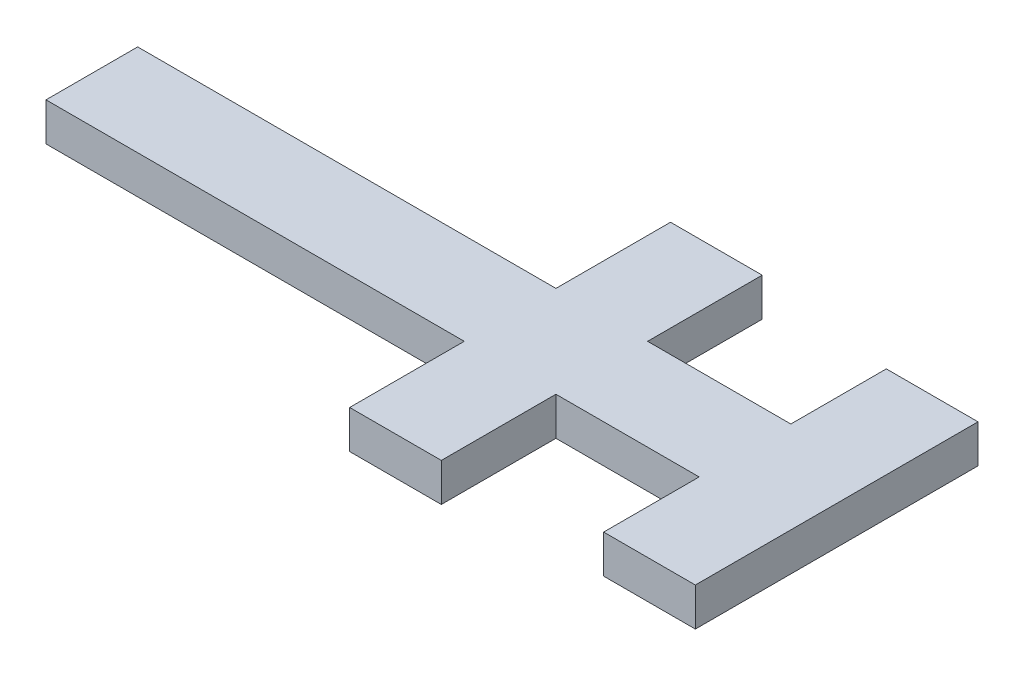
SolidWorks part; units mm, degrees
ref_plane "前视基准面" through (0, 0, 0) normal (0, 0, 1) x (1, 0, 0)
ref_plane "上视基准面" through (0, 0, 0) normal (0, 1, 0) x (1, 0, 0)
ref_plane "右视基准面" through (0, 0, 0) normal (1, 0, 0) x (0, 0, -1)
other "Configuration Table"
sketch "草图2" plane through (0, 0, 0) normal (0, 1, 0) x (1, 0, 0)
  line L0 (0, 0) -> (-31, 0) construction
  line L5 (-12.5, -5) -> (12.5, -5)
  line L6 (-12.5, -5) -> (-12.5, 5)
  line L7 (-12.5, 5) -> (12.5, 5)
  line L8 (12.5, -5) -> (12.5, 5)
  line L9 (-12.5, -5) -> (12.5, 5) construction
  line L10 (-12.5, 5) -> (12.5, -5) construction
  line L11 (17.5, 0) -> (12.5, 0) construction
  line L12 (-14, -5) -> (-48, -5)
  line L13 (-14, -5) -> (-14, 5)
  line L14 (-14, 5) -> (-48, 5)
  line L15 (-48, -5) -> (-48, 5)
  line L16 (-14, -5) -> (-48, 5) construction
  line L17 (-14, 5) -> (-48, -5) construction
  line L18 (-8.25, -20) -> (-18.25, -20)
  line L19 (-8.25, -20) -> (-8.25, 20)
  line L20 (-8.25, 20) -> (-18.25, 20)
  line L21 (-18.25, -20) -> (-18.25, 20)
  line L22 (-8.25, -20) -> (-18.25, 20) construction
  line L23 (-8.25, 20) -> (-18.25, -20) construction
  line L24 (22.5, -17.5) -> (12.5, -17.5)
  line L25 (22.5, -17.5) -> (22.5, 17.5)
  line L26 (22.5, 17.5) -> (12.5, 17.5)
  line L27 (12.5, -17.5) -> (12.5, 17.5)
  line L28 (22.5, -17.5) -> (12.5, 17.5) construction
  line L29 (22.5, 17.5) -> (12.5, -17.5) construction
  line L31 (-48, 5) -> (-73, 5)
  line L32 (-48, 5) -> (-48, -5)
  line L33 (-48, -5) -> (-73, -5)
  line L34 (-73, 5) -> (-73, -5)
  point P0 (0, 0)
  point P13 (17.5, 0)
  point P15 (-13.25, 0)
  dimension "D1" = 10
  dimension "D2" = 25
  dimension "D3" = 34
  dimension "D4" = 10
  dimension "D5" = 31
  dimension "D6" = 10
  dimension "D7" = 0.75
  dimension "D8" = 40
  dimension "D9" = 10
  dimension "D10" = 5
  dimension "D11" = 35
  dimension "D12" = 25
sketch "草图3" plane through (0, 0, 0) normal (0, 1, 0) x (1, 0, 0)
  line L0 (-12.5, -5) -> (12.5, -5) construction
  line L1 (22.5, 17.5) -> (12.5, 17.5)
  line L2 (22.5, 17.5) -> (22.5, -17.5)
  line L3 (22.5, -17.5) -> (12.5, -17.5)
  line L4 (12.5, 17.5) -> (12.5, -17.5)
  line L5 (12.5, 5) -> (-8.25, 5)
  line L6 (12.5, 5) -> (12.5, -5)
  line L7 (12.5, -5) -> (-8.25, -5)
  line L8 (-8.25, 5) -> (-8.25, -5)
  line L9 (-8.25, -20) -> (-8.25, 20) construction
  line L10 (-14, 5) -> (-48, 5) construction
  line L11 (-8.25, 20) -> (-18.25, 20)
  line L12 (-8.25, 20) -> (-8.25, -20)
  line L13 (-8.25, -20) -> (-18.25, -20)
  line L14 (-18.25, 20) -> (-18.25, -20)
  line L15 (-48, -5) -> (-18.25, -5)
  line L16 (-48, -5) -> (-48, 5)
  line L17 (-48, 5) -> (-18.25, 5)
  line L18 (-18.25, -5) -> (-18.25, 5)
  line L20 (-48, 5) -> (-73, 5)
  line L21 (-48, 5) -> (-48, -5)
  line L22 (-48, -5) -> (-73, -5)
  line L23 (-73, 5) -> (-73, -5)
extrude "凸台-拉伸1" add sketch "草图3" along normal blind 1 contours L1 L4 L3 L2 | L5 L8 L7 L4 | L11 L14 L13 L12 L8 | L17 L16 L15 L14 | L20 L23 L22 L16
sketch "草图4" plane through (0, 0, 0) normal (0, -1, 0) x (1, 0, 0)
  line L0 (11.5, -18.5) -> (23.5, -18.5)
  line L1 (23.5, -18.5) -> (23.5, 18.5)
  line L2 (23.5, 18.5) -> (11.5, 18.5)
  line L3 (11.5, 18.5) -> (11.5, 6)
  line L4 (11.5, 6) -> (-7.25, 6)
  line L5 (-7.25, 6) -> (-7.25, 21)
  line L6 (-7.25, 21) -> (-19.25, 21)
  line L7 (-19.25, 21) -> (-19.25, 6)
  line L8 (-19.25, 6) -> (-74, 6)
  line L9 (-74, 6) -> (-74, -6)
  line L10 (-74, -6) -> (-19.25, -6)
  line L11 (-19.25, -6) -> (-19.25, -21)
  line L12 (-19.25, -21) -> (-7.25, -21)
  line L13 (-7.25, -21) -> (-7.25, -6)
  line L14 (-7.25, -6) -> (11.5, -6)
  line L15 (11.5, -6) -> (11.5, -18.5)
  line L16 (12.5, -17.5) -> (22.5, -17.5)
  line L17 (22.5, -17.5) -> (22.5, 17.5)
  line L18 (22.5, 17.5) -> (12.5, 17.5)
  line L19 (12.5, 17.5) -> (12.5, 5)
  line L20 (12.5, 5) -> (-8.25, 5)
  line L21 (-8.25, 5) -> (-8.25, 20)
  line L22 (-8.25, 20) -> (-18.25, 20)
  line L23 (-18.25, 20) -> (-18.25, 5)
  line L24 (-18.25, 5) -> (-73, 5)
  line L25 (-73, 5) -> (-73, -5)
  line L26 (-73, -5) -> (-18.25, -5)
  line L27 (-18.25, -5) -> (-18.25, -20)
  line L28 (-18.25, -20) -> (-8.25, -20)
  line L29 (-8.25, -20) -> (-8.25, -5)
  line L30 (-8.25, -5) -> (12.5, -5)
  line L31 (12.5, -5) -> (12.5, -17.5)
  line L32 (12.5, -17.5) -> (22.5, -17.5)
  line L33 (22.5, -17.5) -> (22.5, 17.5)
  line L34 (22.5, 17.5) -> (12.5, 17.5)
  line L35 (12.5, 17.5) -> (12.5, 5)
  line L36 (12.5, 5) -> (-8.25, 5)
  line L37 (-8.25, 5) -> (-8.25, 20)
  line L38 (-8.25, 20) -> (-18.25, 20)
  line L39 (-18.25, 20) -> (-18.25, 5)
  line L40 (-18.25, 5) -> (-73, 5)
  line L41 (-73, 5) -> (-73, -5)
  line L42 (-73, -5) -> (-18.25, -5)
  line L43 (-18.25, -5) -> (-18.25, -20)
  line L44 (-18.25, -20) -> (-8.25, -20)
  line L45 (-8.25, -20) -> (-8.25, -5)
  line L46 (-8.25, -5) -> (12.5, -5)
  line L47 (12.5, -5) -> (12.5, -17.5)
  dimension "D1" = 0
  dimension "D2" = 1
extrude "凸台-拉伸2" add sketch "草图4" along normal blind 4 and the other way blind 1
sketch "草图5" plane through (0, 0, 0) normal (0, -1, 0) x (1, 0, 0)
  line L0 (-18.25, 20) -> (-18.25, 5)
  line L1 (-73, 5) -> (-48, 5)
  line L2 (-73, 5) -> (-73, -5)
  line L3 (-73, -5) -> (-48, -5)
  line L4 (-48, 5) -> (-48, -5)
  line L5 (12.5, 17.5) -> (22.5, 17.5)
  line L6 (12.5, 17.5) -> (12.5, -17.5)
  line L7 (12.5, -17.5) -> (22.5, -17.5)
  line L8 (22.5, 17.5) -> (22.5, -17.5)
  line L9 (-18.25, 5) -> (-14, 5)
  line L10 (-14, 5) -> (-14, -5)
  line L11 (-14, -5) -> (-18.25, -5)
  line L12 (-18.25, -5) -> (-18.25, -20)
  line L13 (-18.25, -20) -> (-8.25, -20)
  line L14 (-8.25, -20) -> (-8.25, -5)
  line L15 (-8.25, -5) -> (-12.5, -5)
  line L16 (-12.5, -5) -> (-12.5, 5)
  line L17 (-12.5, 5) -> (-8.25, 5)
  line L18 (-8.25, 5) -> (-8.25, 20)
  line L19 (-8.25, 20) -> (-18.25, 20)
extrude "凸台-拉伸3" add sketch "草图5" along normal blind 2
